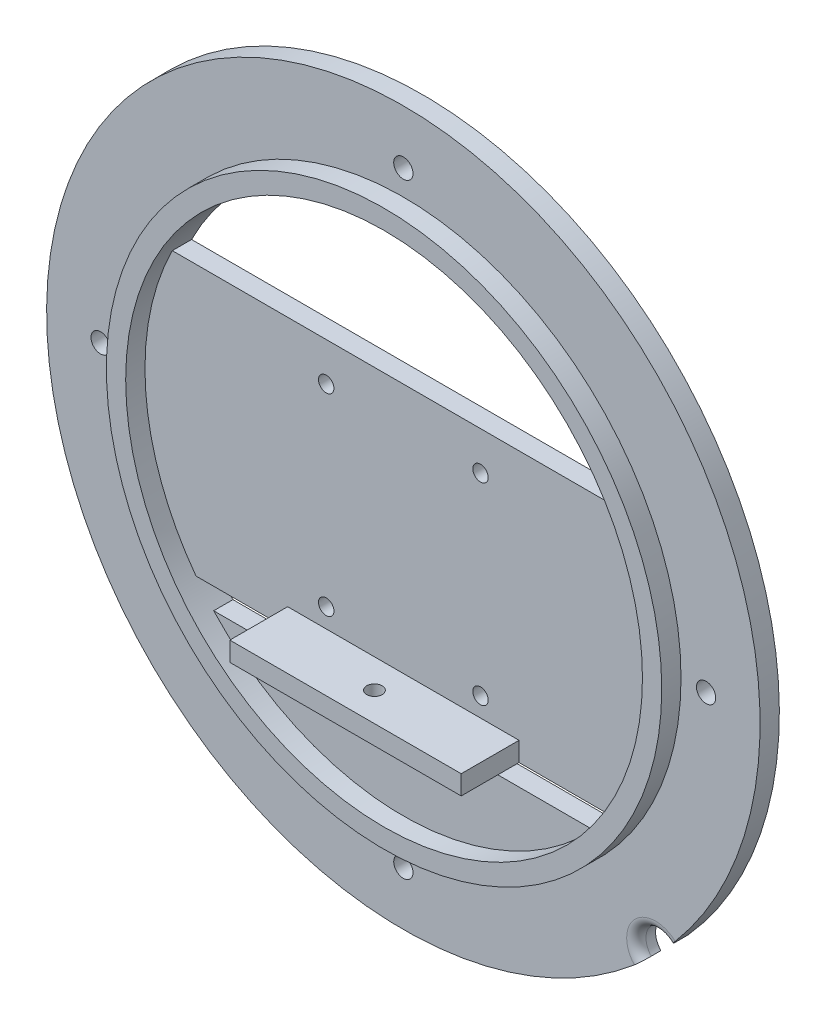
SolidWorks part; units mm, degrees
ref_plane "Front Plane" through (0, 0, 0) normal (0, 0, 1) x (1, 0, 0)
ref_plane "Top Plane" through (0, 0, 0) normal (0, 1, 0) x (1, 0, 0)
ref_plane "Right Plane" through (0, 0, 0) normal (1, 0, 0) x (0, 0, -1)
sketch "Sketch1" plane through (0, 0, 0) normal (0, 0, 1) x (1, 0, 0)
  circle A0 centre (0, 0) radius 92.5
  dimension "D1" = 185
extrude "Boss-Extrude1" add sketch "Sketch1" along normal blind 5
sketch "Sketch2" plane through (0, 0, 5) normal (0, 0, 1) x (1, 0, 0)
  circle A0 centre (0, 0) radius 72
  dimension "D1" = 144
extrude "Boss-Extrude2" add sketch "Sketch2" along normal blind 5
sketch "Sketch3" plane through (0, 0, 0) normal (0, 0, -1) x (-1, 0, 0)
  circle A0 centre (0, 0) radius 67
  dimension "D1" = 134
extrude "Cut-Extrude1" cut sketch "Sketch3" against normal through all
sketch "Sketch4" plane through (0, 0, 0) normal (0, 0, -1) x (-1, 0, 0)
  line L0 (92.5, 0) -> (-92.5, 0) construction
  line L5 (0, -92.5) -> (0, 92.5) construction
  line L11 (70, 30) -> (-70, 30)
  line L12 (70, 30) -> (70, -40)
  line L13 (70, -40) -> (-70, -40)
  line L14 (-70, 30) -> (-70, -40)
  circle A0 centre (0, 0) radius 92.5 construction
  dimension "D1" = 70
  dimension "D2" = 40
  dimension "D3" = 30
  dimension "D4" = 140
  dimension "D5" = 70
  dimension "D6" = 70
extrude "Boss-Extrude3" add sketch "Sketch4" against normal blind 5
sketch "Sketch6" plane through (0, 0, 5) normal (0, 0, 1) x (1, 0, 0)
  line L0 (0, -40) -> (0, 30) construction
  line L1 (53.7494, -40) -> (-53.7494, -40) construction
  line L2 (-59.9083, 30) -> (59.9083, 30) construction
  line L3 (-92.5, 0) -> (92.5, 0) construction
  line L5 (30, -40) -> (-30, -40)
  line L6 (30, -40) -> (30, -35)
  line L7 (30, -35) -> (-30, -35)
  line L8 (-30, -40) -> (-30, -35)
  circle A0 centre (0, 0) radius 92.5 construction
  dimension "D1" = 30
  dimension "D2" = 60
  dimension "D3" = 30
  dimension "D4" = 5
fillet "Fillet1" radius 2.5 1 edges at (0, -40, 0)
sketch "Sketch7" plane through (0, 0, 0) normal (0, 0, -1) x (-1, 0, 0)
  line L0 (0, 92.5) -> (0, -92.5) construction
  line L1 (92.5, 0) -> (-92.5, 0) construction
  line L2 (53.7494, -40) -> (-53.7494, -40) construction
  line L3 (-55, -45.5) -> (55, -45.5)
  line L4 (-55, -45.5) -> (-55, -70.5)
  line L5 (-55, -70.5) -> (55, -70.5)
  line L6 (55, -45.5) -> (55, -70.5)
  circle A0 centre (0, 0) radius 92.5 construction
  dimension "D1" = 110
  dimension "D2" = 8
  dimension "D3" = 25
  dimension "D4" = 55
  dimension "D5" = 5.5
extrude "Boss-Extrude5" add sketch "Sketch7" against normal blind 5
sketch "Sketch11" plane through (0, 0, 0) normal (0, 0, -1) x (-1, 0, 0)
  line L0 (-92.5, 0) -> (92.5, 0) construction
  line L1 (0, -92.5) -> (0, 90.9687) construction
  line L2 (70, 30) -> (-70, 30) construction
  circle A0 centre (0, 0) radius 92.5 construction
  circle A1 centre (-20, -30) radius 2
  circle A2 centre (-20, 20) radius 2
  circle A3 centre (20, 20) radius 2
  circle A4 centre (20, -30) radius 2
  dimension "D7" = 4
  dimension "D8" = 4
  dimension "D9" = 4
  dimension "D10" = 4
  dimension "D1" = 40
  dimension "D2" = 20
  dimension "D3" = 20
  dimension "D4" = 20
  dimension "D5" = 20
  dimension "D6" = 20
  dimension "D11" = 40
  dimension "D12" = 50
  dimension "D13" = 50
  dimension "D14" = 10
  dimension "D15" = 10
extrude "Cut-Extrude4" cut sketch "Sketch11" against normal up to surface (5 mm away) up to face at (0, -5.4361, 5)
sketch "Sketch12" plane through (0, 0, 0) normal (0, 0, -1) x (-1, 0, 0)
  line L0 (0, -92.5) -> (0, 92.5) construction
  line L1 (92.5, 0) -> (-92.5, 0) construction
  circle A0 centre (0, 0) radius 92.5 construction
  circle A1 centre (0, -78.5) radius 2.5
  circle A2 centre (-78.5, 0) radius 2.5
  circle A3 centre (0, 78.5) radius 2.5
  circle A4 centre (78.5, 0) radius 2.5
  dimension "D1" = 5
  dimension "D2" = 5
  dimension "D3" = 5
  dimension "D4" = 5
  dimension "D5" = 78.5
  dimension "D6" = 78.5
  dimension "D7" = 78.5
  dimension "D8" = 78.5
extrude "Cut-Extrude5" cut sketch "Sketch12" against normal up to surface (5 mm away) up to face at (72, 0, 5)
extrude "Boss-Extrude6" add sketch "Sketch6" along normal blind 15
sketch "Sketch13" plane through (0, -40, 0) normal (0, -1, 0) x (1, 0, 0)
  line L0 (0, 20) -> (0, 0) construction
  line L1 (-30, 20) -> (30, 20) construction
  line L2 (-70, 0) -> (70, 0) construction
  circle A0 centre (0, 12.5) radius 2
  dimension "D2" = 4
  dimension "D1" = 7.5
extrude "Cut-Extrude6" cut sketch "Sketch13" against normal up to surface (5 mm away) up to face at (0, -35, 12.5)
sketch "Sketch14" plane through (0, 0, 0) normal (0, 0, -1) x (-1, 0, 0)
  line L1 (0, 0) -> (-65.4074, -65.4074) construction
  line L2 (92.5, 0) -> (-92.5, 0) construction
  circle A1 centre (0, 0) radius 92.5 construction
  circle A2 centre (-65.4074, -65.4074) radius 5
  dimension "D2" = 10
  dimension "D1" = 45
extrude "Cut-Extrude7" cut sketch "Sketch14" against normal blind 10
fillet "Fillet2" radius 2.5 1 edges at (61.8718, -61.8718, 5)
